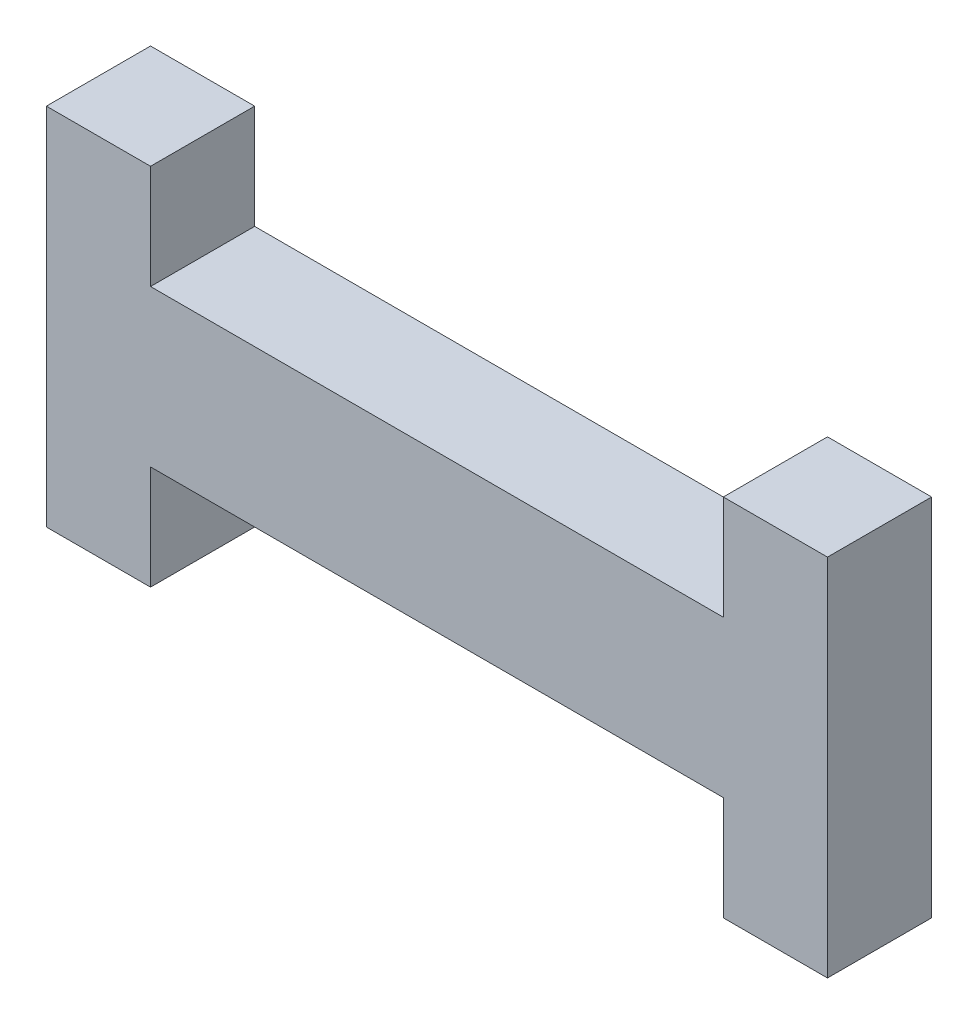
SolidWorks part; units mm, degrees
ref_plane "Plan de face" through (0, 0, 0) normal (0, 0, 1) x (1, 0, 0)
ref_plane "Plan de dessus" through (0, 0, 0) normal (0, 1, 0) x (1, 0, 0)
ref_plane "Plan de droite" through (0, 0, 0) normal (1, 0, 0) x (0, 0, -1)
sketch "Esquisse1" plane through (0, 0, 0) normal (0, 0, 1) x (1, 0, 0)
  line L0 (0, 0) -> (11, 0)
  line L1 (11, 0) -> (11, 2)
  line L2 (11, 2) -> (13, 2)
  line L3 (13, 2) -> (13, -5)
  line L4 (13, -5) -> (11, -5)
  line L5 (11, -5) -> (11, -3)
  line L6 (11, -3) -> (0, -3)
  line L7 (0, -3) -> (0, -5)
  line L8 (0, -5) -> (-2, -5)
  line L9 (-2, -5) -> (-2, 2)
  line L10 (-2, 2) -> (0, 2)
  line L11 (0, 2) -> (0, 0)
  dimension "D1" = 3
  dimension "D2" = 7
  dimension "D3" = 7
  dimension "D4" = 2
  dimension "D5" = 2
  dimension "D6" = 2
  dimension "D7" = 2
  dimension "D8" = 11
extrude "Boss.-Extru.1" add sketch "Esquisse1" along normal blind 2
